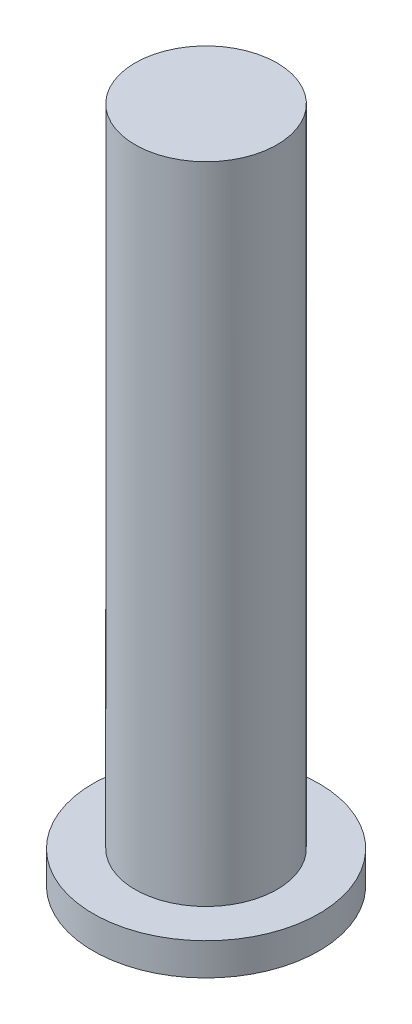
SolidWorks part; units mm, degrees
ref_plane "前视基准面" through (0, 0, 0) normal (0, 0, 1) x (1, 0, 0)
ref_plane "上视基准面" through (0, 0, 0) normal (0, 1, 0) x (1, 0, 0)
ref_plane "右视基准面" through (0, 0, 0) normal (1, 0, 0) x (0, 0, -1)
sketch "草图2" plane through (0, 0, 0) normal (0, -1, 0) x (1, 0, 0)
  circle A1 centre (96.9527, -8.6831) radius 3.5
  circle A2 centre (96.9527, -8.6831) radius 1.65
  dimension "D1" = 3.3
  dimension "D2" = 7
extrude "凸台-拉伸1" add sketch "草图2" along normal blind 1
sketch "草图3" plane through (0, 0, 0) normal (0, 1, 0) x (1, 0, 0)
  circle A0 centre (96.9527, 8.6831) radius 2.2
  dimension "D1" = 4.4
extrude "凸台-拉伸2" add sketch "草图3" along normal blind 20
sketch "草图6" plane through (0, 0, 0) normal (0, -1, 0) x (1, 0, 0)
  circle A1 centre (96.9527, -8.6831) radius 1.65
  circle A2 centre (96.9527, -8.6831) radius 1.65
  dimension "D1" = 0
extrude "切除-拉伸1" cut sketch "草图6" against normal blind 10
